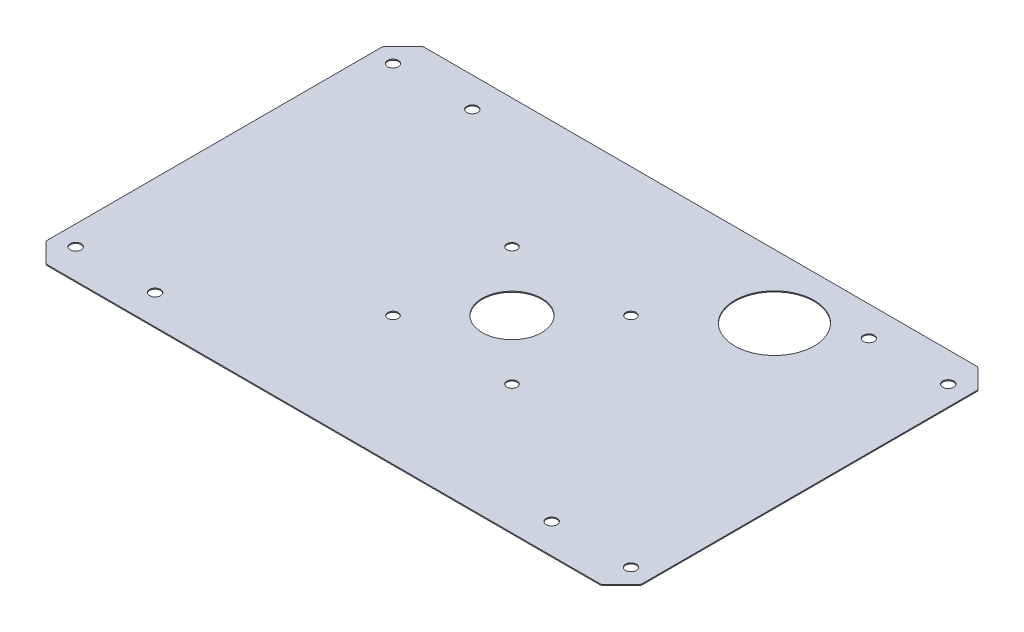
SolidWorks part; units mm, degrees
ref_plane "Plan de face" through (0, 0, 0) normal (0, 0, 1) x (1, 0, 0)
ref_plane "Plan de dessus" through (0, 0, 0) normal (0, 1, 0) x (1, 0, 0)
ref_plane "Plan de droite" through (0, 0, 0) normal (1, 0, 0) x (0, 0, -1)
sketch "Esquisse1" plane through (0, 0, 0) normal (0, 1, 0) x (1, 0, 0)
  line L1 (-150, -95) -> (150, -95)
  line L2 (-150, -95) -> (-150, 95)
  line L3 (-150, 95) -> (150, 95)
  line L4 (150, -95) -> (150, 95)
  line L5 (-150, -95) -> (150, 95) construction
  line L6 (-150, 95) -> (150, -95) construction
  point P0 (0, 0)
  dimension "D1" = 300
  dimension "D2" = 190
extrude "Boss.-Extru.1" add sketch "Esquisse1" along normal blind 0.5
chamfer "Chanfrein1" distance 10 angle 45 4 edges at (-150, 0.25, 95) (150, 0.25, 95) (150, 0.25, -95) (-150, 0.25, -95)
fillet "Congé1" radius 2 8 edges at (-150, 0.25, -85) (-140, 0.25, -95) (140, 0.25, -95) (150, 0.25, -85) (150, 0.25, 85) (140, 0.25, 95) (-140, 0.25, 95) (-150, 0.25, 85)
sketch "Esquisse2" plane through (0, 0, 0) normal (0, -1, 0) x (1, 0, 0)
  line L0 (-140, 80) -> (-100, 80) construction
  line L3 (-150, -84.1716) -> (-150, 84.1716) construction
  line L4 (-139.1716, 95) -> (139.1716, 95) construction
  circle A0 centre (-140, 80) radius 2.75
  circle A1 centre (-100, 80) radius 2.75
  point P4 (-120, 80)
  dimension "D1" = 5.5
  dimension "D2" = 40
  dimension "D3" = 10
  dimension "D4" = 15
extrude "Enlèv. mat.-Extru.1" cut sketch "Esquisse2" against normal through all
pattern_linear "Répétition linéaire1" count 2 spacing 240 along (1, 0, 0) count 2 spacing 160 along (0, 0, -1) of "Enlèv. mat.-Extru.1"
sketch "Esquisse4" plane through (0, 0.5, 0) normal (0, 1, 0) x (1, 0, 0)
  line L0 (59.1, 75) -> (80, 50.6) construction
  circle A0 centre (59.1, 75) radius 1.6 construction
  circle A1 centre (80, 50.6) radius 1.6 construction
  circle A2 centre (100, 80) radius 2.75 construction
  circle A3 centre (100, 80) radius 2.75
  circle A4 centre (69.55, 62.8) radius 20
  circle A6 centre (0, 0) radius 15
  point P7 (69.55, 62.8)
  dimension "D1" = 3.2
  dimension "D4" = 20
  dimension "D6" = 40
  dimension "D7" = 30
  dimension "D2" = 24.4
  dimension "D3" = 20.9
  dimension "D5" = 5
extrude "Enlèv. mat.-Extru.3" cut sketch "Esquisse4" against normal blind 10
sketch "Esquisse5" plane through (0, 0.5, 0) normal (0, 1, 0) x (1, 0, 0)
  line L1 (-30, -30) -> (30, -30) construction
  line L2 (-30, -30) -> (-30, 30) construction
  line L3 (-30, 30) -> (30, 30) construction
  line L4 (30, -30) -> (30, 30) construction
  line L5 (-30, -30) -> (30, 30) construction
  line L6 (-30, 30) -> (30, -30) construction
  circle A0 centre (-30, 30) radius 2.6
  circle A1 centre (30, 30) radius 2.6
  circle A2 centre (30, -30) radius 2.6
  circle A3 centre (-30, -30) radius 2.6
  point P0 (0, 0)
  dimension "D2" = 5.2
  dimension "D1" = 60
extrude "Enlèv. mat.-Extru.4" cut sketch "Esquisse5" against normal through all
